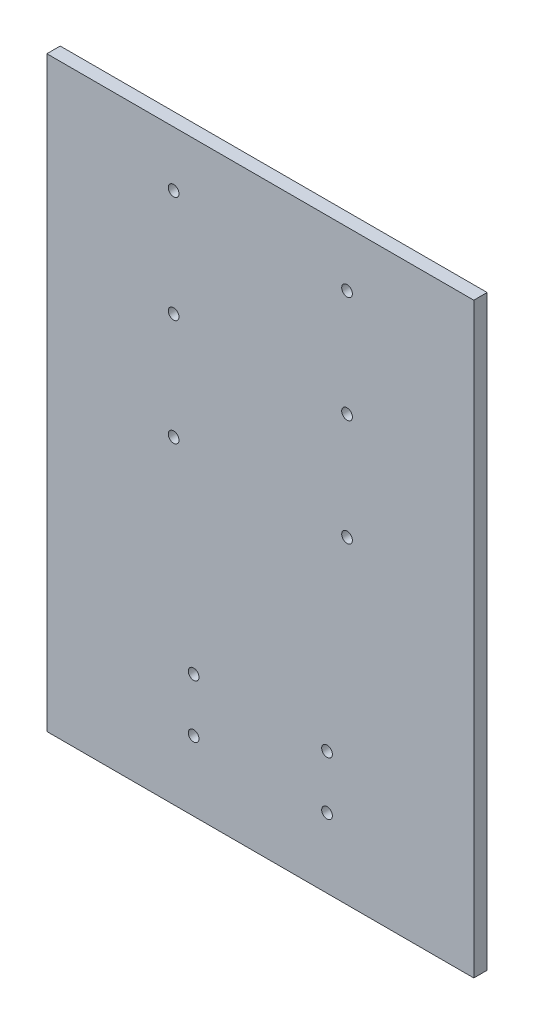
SolidWorks part; units mm, degrees
ref_plane "Front Plane" through (0, 0, 0) normal (0, 0, 1) x (1, 0, 0)
ref_plane "Top Plane" through (0, 0, 0) normal (0, 1, 0) x (1, 0, 0)
ref_plane "Right Plane" through (0, 0, 0) normal (1, 0, 0) x (0, 0, -1)
sketch "Sketch1" plane through (0, 0, 0) normal (0, 0, 1) x (1, 0, 0)
  line L1 (0, 0) -> (203.2, 0)
  line L2 (0, 0) -> (0, 279.4)
  line L3 (0, 279.4) -> (203.2, 279.4)
  line L4 (203.2, 0) -> (203.2, 279.4)
  dimension "D1" = 279.4
  dimension "D2" = 203.2
extrude "Boss-Extrude1" add sketch "Sketch1" along normal blind 6.35
sketch "Sketch2" plane through (0, 0, 0) normal (0, 0, 1) x (1, 0, 0)
  point P0 (69.85, 33.1679)
  point P1 (133.35, 33.1679)
  point P3 (133.35, 58.5679)
  point P5 (69.85, 58.5679)
  point P7 (60.325, 151.5229)
  point P9 (142.875, 151.5229)
  point P11 (142.875, 202.3229)
  point P13 (60.325, 202.3229)
  point P15 (60.325, 253.1229)
  point P17 (142.875, 253.1229)
  point P19 (0, 279.4)
hole_wizard "1/4-20 Tapped Hole1" positions "Sketch4" profile "Sketch3" tap size "1/4-20" standard "ANSI Inch"
sketch "Sketch4" plane through (0, 0, 0) normal (0, 0, -1) x (-1, 0, 0)
  point P0 (-60.325, 253.1229)
  point P3 (-142.875, 253.1229)
  point P6 (-142.875, 202.3229)
  point P9 (-142.875, 151.5229)
  point P12 (-60.325, 151.5229)
  point P15 (-60.325, 202.3229)
  point P18 (-133.35, 58.5679)
  point P21 (-133.35, 33.1679)
  point P24 (-69.85, 33.1679)
  point P27 (-69.85, 58.5679)
sketch "Sketch3" plane through (60.325, 253.1229, 0) normal (1, 0, 0) x (0, 1, 0)
  line L0 (0, 0) -> (0, 10.3451)
  line L1 (0, 10.3451) -> (2.5527, 8.8113)
  line L2 (2.5527, 8.8113) -> (2.5527, 0)
  line L5 (2.5527, 0) -> (0, 0)
  line L10 (0, 10.3451) -> (-2.5527, 8.8113) construction
  line L11 (0, -6.35) -> (0, 107.95) construction
  dimension "Tap Drill Dia." = 5.1054
  dimension "Tap Drill Depth" = 8.8113
  dimension "Drill Angle" = 118
